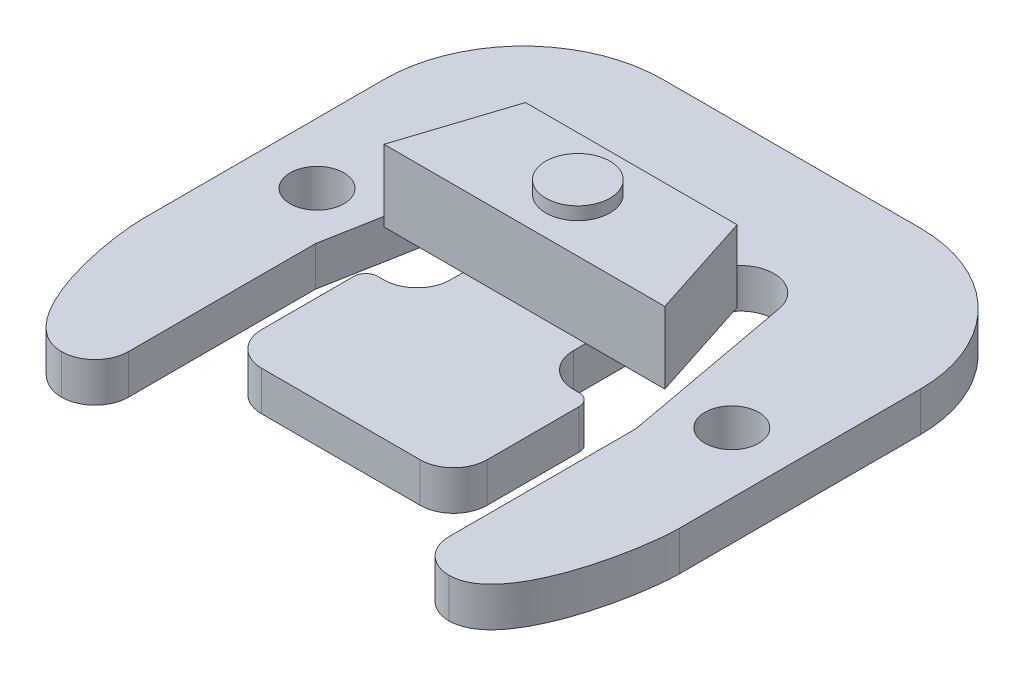
SolidWorks part; units mm, degrees
ref_plane "Front Plane" through (0, 0, 0) normal (0, 0, 1) x (1, 0, 0)
ref_plane "Top Plane" through (0, 0, 0) normal (0, 1, 0) x (1, 0, 0)
ref_plane "Right Plane" through (0, 0, 0) normal (1, 0, 0) x (0, 0, -1)
sketch "Sketch1" plane through (0, 0, 0) normal (0, 1, 0) x (1, 0, 0)
  line L0 (27.1272, -31.8389) -> (27.1272, -19.9898)
  line L1 (8.8138, 0) -> (25.146, 0)
  line L2 (0, -8.8138) -> (0, -24.0874)
  line L3 (0, -33.9598) -> (4.7117, -33.9598) construction
  line L4 (33.9598, -8.8138) -> (33.9598, -24.0874)
  line L5 (27.1272, -19.9898) -> (25.0727, -8.8606)
  line L6 (20.8661, -9.2456) -> (20.8661, -17.7038)
  line L7 (22.987, -19.8247) -> (23.3553, -19.8247)
  line L8 (21.9964, -28.5369) -> (11.9634, -28.5369)
  line L9 (24.1173, -20.5867) -> (24.1173, -26.416)
  line L10 (16.9799, -1000) -> (16.9799, 49000) construction
  line L11 (9.8425, -20.5867) -> (9.8425, -26.416)
  line L12 (10.9728, -19.8247) -> (10.6045, -19.8247)
  line L13 (13.0937, -9.2456) -> (13.0937, -17.7038)
  line L14 (6.8326, -19.9898) -> (8.8871, -8.8606)
  line L15 (6.8326, -31.8389) -> (6.8326, -19.9898)
  line L16 (29.2481, -33.9598) -> (33.9598, -33.9598) construction
  line L17 (0, -28.1505) -> (0, -19.8805) construction
  line L18 (9.1752, -33.9598) -> (-0.2304, -33.9598) construction
  arc A0 (25.146, 0) -> (33.9598, -8.8138) centre (25.146, -8.8138) cw
  arc A1 (8.8138, 0) -> (0, -8.8138) centre (8.8138, -8.8138) ccw
  arc A2 (25.0727, -8.8606) -> (20.8661, -9.2456) centre (22.987, -9.2456) ccw
  arc A3 (8.8871, -8.8606) -> (13.0937, -9.2456) centre (10.9728, -9.2456) cw
  arc A4 (27.1272, -31.8389) -> (29.2481, -33.9598) centre (29.2481, -31.8389) ccw
  arc A5 (6.8326, -31.8389) -> (4.7117, -33.9598) centre (4.7117, -31.8389) cw
  arc A6 (20.8661, -17.7038) -> (22.987, -19.8247) centre (22.987, -17.7038) ccw
  arc A7 (10.9728, -19.8247) -> (13.0937, -17.7038) centre (10.9728, -17.7038) ccw
  arc A8 (24.1173, -26.416) -> (21.9964, -28.5369) centre (21.9964, -26.416) cw
  arc A9 (9.8425, -26.416) -> (11.9634, -28.5369) centre (11.9634, -26.416) ccw
  arc A10 (23.3553, -19.8247) -> (24.1173, -20.5867) centre (23.3553, -20.5867) cw
  arc A11 (9.8425, -20.5867) -> (10.6045, -19.8247) centre (10.6045, -20.5867) cw
  circle A12 centre (30.1117, -16.9164) radius 1.7018
  circle A13 centre (3.8481, -16.9164) radius 1.7018
  spline S0 degree 3 poles (0, -24.0874) (0, -26.5171) (1.3692, -33.9598) (4.7117, -33.9598) knots 0 0 0 0 1 1 1 1
  spline S1 degree 3 poles (33.9598, -24.0874) (33.9598, -26.5171) (32.5906, -33.9598) (29.2481, -33.9598) knots 0 0 0 0 1 1 1 1
  point P7 (33.9598, 0)
  point P10 (0, 0)
  point P24 (16.9799, 0)
  point P29 (16.9799, -28.5369)
  point P33 (27.1272, -33.9598)
  point P36 (6.8326, -33.9598)
  point P39 (20.8661, -19.8247)
  point P42 (13.0937, -19.8247)
  point P45 (24.1173, -28.5369)
  point P48 (9.8425, -28.5369)
  point P51 (24.1173, -19.8247)
  point P54 (9.8425, -19.8247)
  dimension "D3" = 8.8138
  dimension "D5" = 2.1209
  dimension "D12" = 2.1209
  dimension "D13" = 2.1209
  dimension "D14" = 0.762
  dimension "D15" = 3.4036
  dimension "D1" = 33.9598
  dimension "D2" = 33.9598
  dimension "D4" = 6.8326
  dimension "D6" = 7.1374
  dimension "D7" = 5.4229
  dimension "D8" = 9.2456
  dimension "D9" = 10.9728
  dimension "D10" = 13.97
  dimension "D11" = 8.7122
  dimension "D16" = 3.8481
  dimension "D17" = 16.9164
extrude "Boss-Extrude1" add sketch "Sketch1" along normal blind 2.5019
sketch "Sketch2" plane through (0, 2.5019, 0) normal (0, 1, 0) x (1, 0, 0)
  line L0 (8.0899, -16.9164) -> (25.8699, -16.9164)
  line L1 (25.8699, -16.9164) -> (23.6791, -10.1473)
  line L2 (23.6791, -10.1473) -> (10.2807, -10.1473)
  line L3 (10.2807, -10.1473) -> (8.0899, -16.9164)
  line L5 (25.146, 0) -> (8.8138, 0) construction
  line L6 (16.9799, 0) -> (16.9799, -16.9164) construction
  point P3 (16.9799, -10.1473)
  dimension "D1" = 17.78
  dimension "D2" = 6.7691
  dimension "D3" = 13.3985
extrude "Boss-Extrude2" add sketch "Sketch2" along normal blind 4.5339
sketch "Sketch3" plane through (0, 7.0358, 0) normal (0, 1, 0) x (-1, 0, 0)
  line L0 (-23.6791, 10.1473) -> (-10.2807, 10.1473) construction
  line L1 (-10.2807, 10.1473) -> (-8.0899, 16.9164) construction
  circle A0 centre (-16.9799, 13.5319) radius 2.032
  point P4 (-16.9799, 10.1473)
  point P7 (-9.1853, 13.5319)
  dimension "D1" = 4.064
extrude "Boss-Extrude3" add sketch "Sketch3" along normal blind 0.8128
sketch "Sketch4" plane through (0, 0, 0) normal (0, -1, 0) x (1, 0, 0)
  line L0 (16.9799, 28.5369) -> (16.9799, -4.1031) construction
  circle A0 centre (13.8948, 24.1676) radius 1.7792
  circle A1 centre (20.065, 24.1676) radius 1.7792
extrude "Boss-Extrude4" add sketch "Sketch4" along normal blind 1.0033
